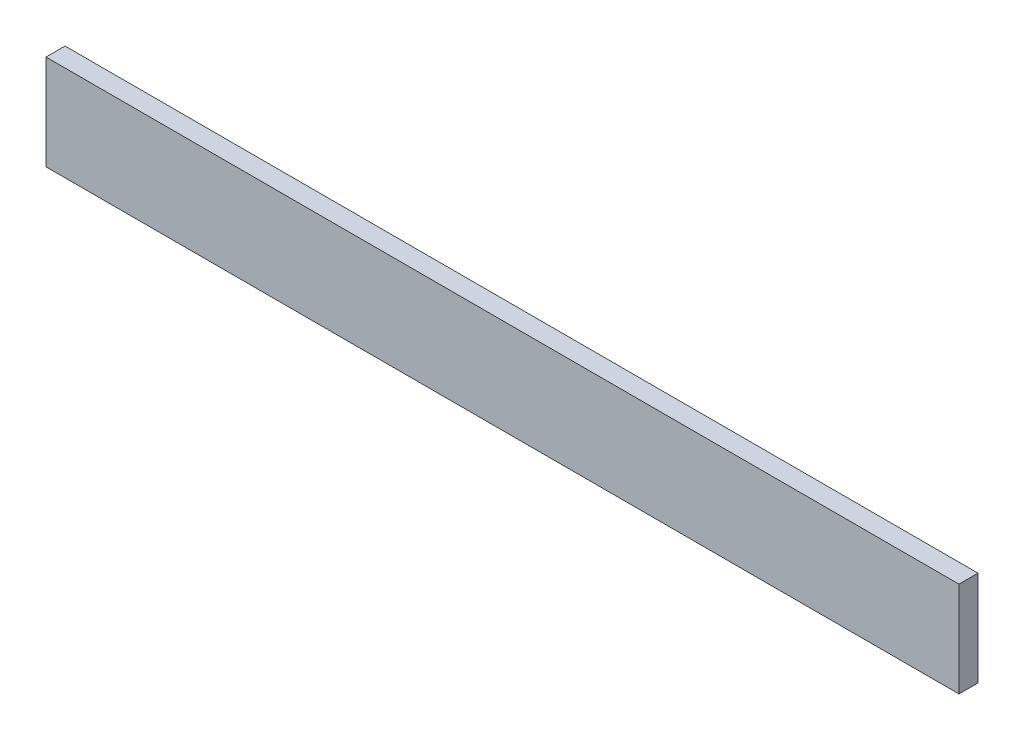
SolidWorks part; units mm, degrees
ref_plane "Front Plane" through (0, 0, 0) normal (0, 0, 1) x (1, 0, 0)
ref_plane "Top Plane" through (0, 0, 0) normal (0, 1, 0) x (1, 0, 0)
ref_plane "Right Plane" through (0, 0, 0) normal (1, 0, 0) x (0, 0, -1)
sketch "Sketch1" plane through (0, 0, 0) normal (0, 0, 1) x (1, 0, 0)
  line L1 (-304.8, -31.75) -> (304.8, -31.75)
  line L2 (-304.8, -31.75) -> (-304.8, 31.75)
  line L3 (-304.8, 31.75) -> (304.8, 31.75)
  line L4 (304.8, -31.75) -> (304.8, 31.75)
  line L5 (-304.8, -31.75) -> (304.8, 31.75) construction
  line L6 (-304.8, 31.75) -> (304.8, -31.75) construction
  point P0 (0, 0)
  dimension "D1" = 63.5
  dimension "D2" = 609.6
extrude "Boss-Extrude1" add sketch "Sketch1" along normal blind 12.7
